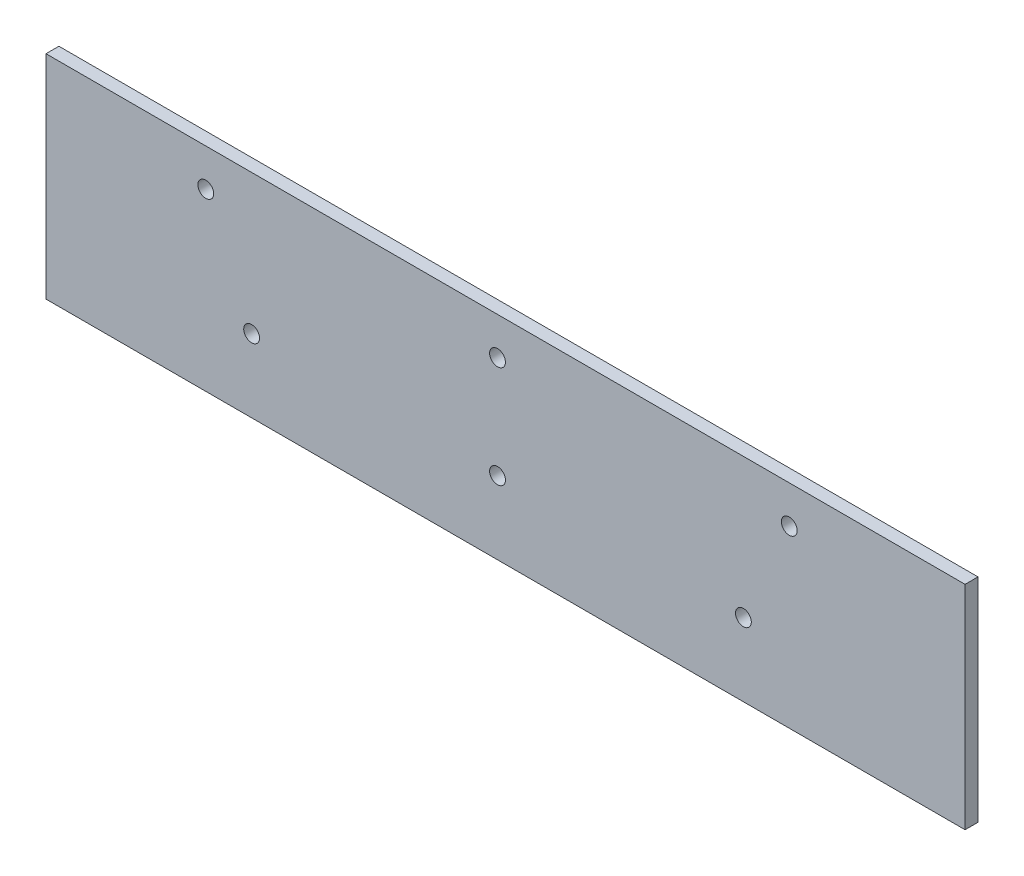
SolidWorks part; units mm, degrees
ref_plane "Front Plane" through (0, 0, 0) normal (0, 0, 1) x (1, 0, 0)
ref_plane "Top Plane" through (0, 0, 0) normal (0, 1, 0) x (1, 0, 0)
ref_plane "Right Plane" through (0, 0, 0) normal (1, 0, 0) x (0, 0, -1)
sketch "Sketch1" plane through (0, 0, 0) normal (0, 0, 1) x (1, 0, 0)
  line L1 (-110.2662, -25.5) -> (110.2662, -25.5)
  line L2 (-110.2662, -25.5) -> (-110.2662, 25.5)
  line L3 (-110.2662, 25.5) -> (110.2662, 25.5)
  line L4 (110.2662, -25.5) -> (110.2662, 25.5)
  line L5 (-110.2662, -25.5) -> (110.2662, 25.5) construction
  line L6 (-110.2662, 25.5) -> (110.2662, -25.5) construction
  point P0 (0, 0)
  dimension "D1" = 51
  dimension "D2" = 220.5325
extrude "Boss-Extrude1" add sketch "Sketch1" along normal blind 3.1
sketch "Sketch2" plane through (0, 0, 3.1) normal (0, 0, 1) x (1, 0, 0)
  point P0 (-71.925, 16.5)
  point P1 (-1.925, 16.5)
  point P3 (68.075, 16.5)
  point P5 (-1.925, -8)
  point P7 (57.075, -8)
  point P9 (-60.925, -8)
hole_wizard "#6 Clearance Hole1" positions "Sketch3" profile "Sketch4" hole size "#6" standard "ANSI Inch" end condition through all
sketch "Sketch3" plane through (0, 0, 3.1) normal (0, 0, 1) x (1, 0, 0)
  point P0 (-71.925, 16.5)
  point P3 (-60.925, -8)
  point P6 (-1.925, -8)
  point P9 (-1.925, 16.5)
  point P12 (68.075, 16.5)
  point P15 (57.075, -8)
sketch "Sketch4" plane through (-71.925, 16.5, 3.1) normal (1, 0, 0) x (0, -1, 0)
  line L0 (0, 0) -> (0, 3.1)
  line L1 (0, 3.1) -> (1.8986, 3.1)
  line L2 (1.8986, 3.1) -> (1.8986, 0)
  line L5 (1.8986, 0) -> (0, 0)
  line L11 (0, -6.35) -> (0, 107.95) construction
  dimension "Thru Hole Dia." = 3.7973
  dimension "Thru Hole Depth" = 3.1
